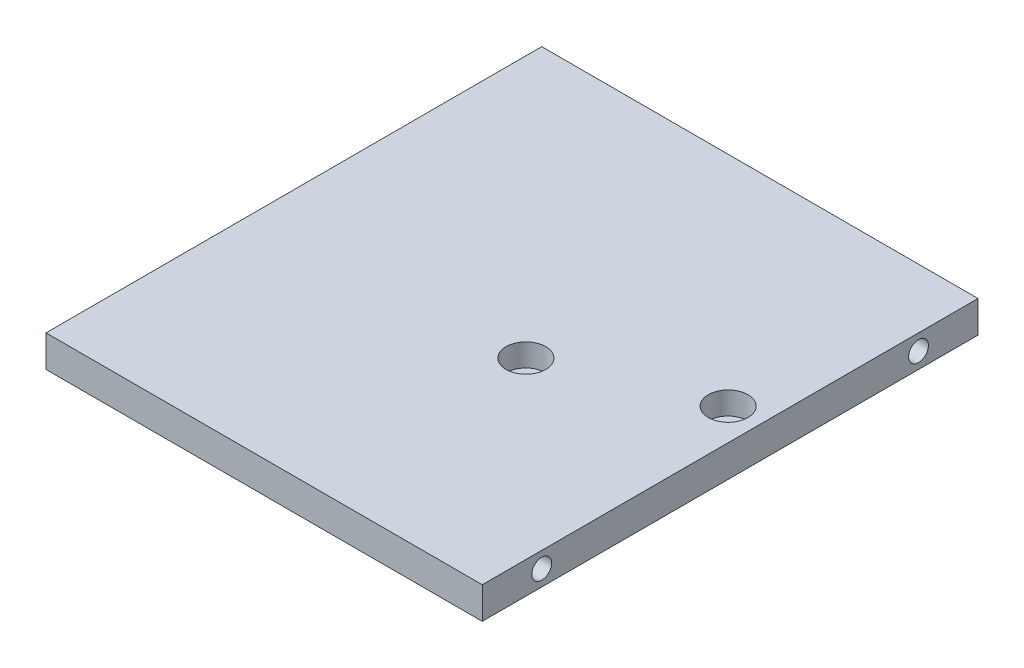
SolidWorks part; units mm, degrees
ref_plane "Front Plane" through (0, 0, 0) normal (0, 0, 1) x (1, 0, 0)
ref_plane "Top Plane" through (0, 0, 0) normal (0, 1, 0) x (1, 0, 0)
ref_plane "Right Plane" through (0, 0, 0) normal (1, 0, 0) x (0, 0, -1)
sketch "Sketch1" plane through (0, 0, 0) normal (0, 1, 0) x (1, 0, 0)
  line L1 (-55, 62.5) -> (55, 62.5)
  line L2 (-55, 62.5) -> (-55, -62.5)
  line L3 (-55, -62.5) -> (55, -62.5)
  line L4 (55, 62.5) -> (55, -62.5)
  line L5 (-55, 62.5) -> (55, -62.5) construction
  line L6 (-55, -62.5) -> (55, 62.5) construction
  point P0 (0, 0)
  dimension "D1" = 125
  dimension "D2" = 110
extrude "Boss-Extrude2" add sketch "Sketch1" along normal blind 8
sketch "Sketch2" plane through (0, 8, 0) normal (0, 1, 0) x (1, 0, 0)
  line L0 (55, 62.5) -> (-55, 62.5) construction
  line L1 (55, -62.5) -> (55, 62.5) construction
  circle A0 centre (47, 7.5) radius 2.75
  circle A1 centre (11, -7.5) radius 2.75
  dimension "D1" = 55
  dimension "D2" = 8
  dimension "D3" = 15
  dimension "D4" = 36
extrude "Cut-Extrude1" cut sketch "Sketch2" against normal blind 8
sketch "Sketch3" plane through (-55, 0, 0) normal (-1, 0, 0) x (0, 0, 1)
  line L0 (-62.5, 8) -> (-62.5, 0) construction
  line L1 (62.5, 8) -> (62.5, 0) construction
  circle A0 centre (47.5, 4) radius 2.5
  circle A1 centre (-47.5, 4) radius 2.5
  dimension "D1" = 15
  dimension "D2" = 15
extrude "Cut-Extrude2" cut sketch "Sketch3" against normal blind 15
sketch "Sketch4" plane through (55, 0, 0) normal (1, 0, 0) x (0, 0, -1)
  line L0 (-62.5, 8) -> (-62.5, 0) construction
  line L1 (62.5, 8) -> (62.5, 0) construction
  circle A0 centre (47.5, 4) radius 2.5
  circle A1 centre (-47.5, 4) radius 2.5
  dimension "D1" = 15
  dimension "D2" = 15
extrude "Cut-Extrude3" cut sketch "Sketch4" against normal blind 15
sketch "Sketch5" plane through (0, 8, 0) normal (0, 1, 0) x (1, 0, 0)
  circle A0 centre (11, -7.5) radius 5
  circle A1 centre (47, 7.5) radius 5
  point P6 (-93.4628, -4.75)
extrude "Cut-Extrude4" cut sketch "Sketch5" against normal blind 5.7
